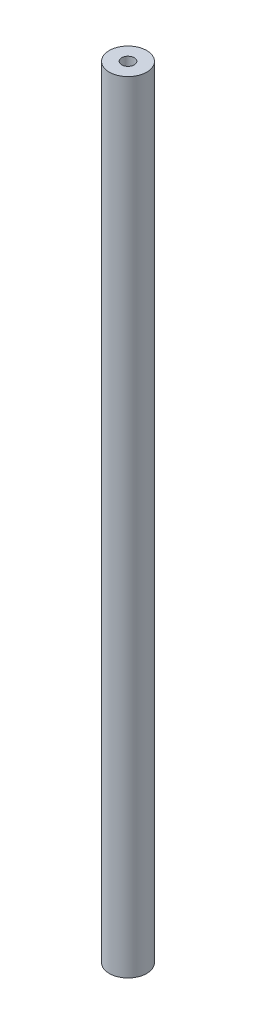
SolidWorks part; units mm, degrees
material "Hexcel AS4C (3000 丝)"
ref_plane "前视基准面" through (0, 0, 0) normal (0, 0, 1) x (1, 0, 0)
ref_plane "上视基准面" through (0, 0, 0) normal (0, 1, 0) x (1, 0, 0)
ref_plane "右视基准面" through (0, 0, 0) normal (1, 0, 0) x (0, 0, -1)
other "Configuration Table"
sketch "草图1" plane through (0, 0, 0) normal (0, 1, 0) x (1, 0, 0)
  circle A0 centre (0, 0) radius 3
  circle A1 centre (0, 0) radius 1
  dimension "D1" = 6
  dimension "D2" = 2
extrude "凸台-拉伸1" add sketch "草图1" along normal blind 125
